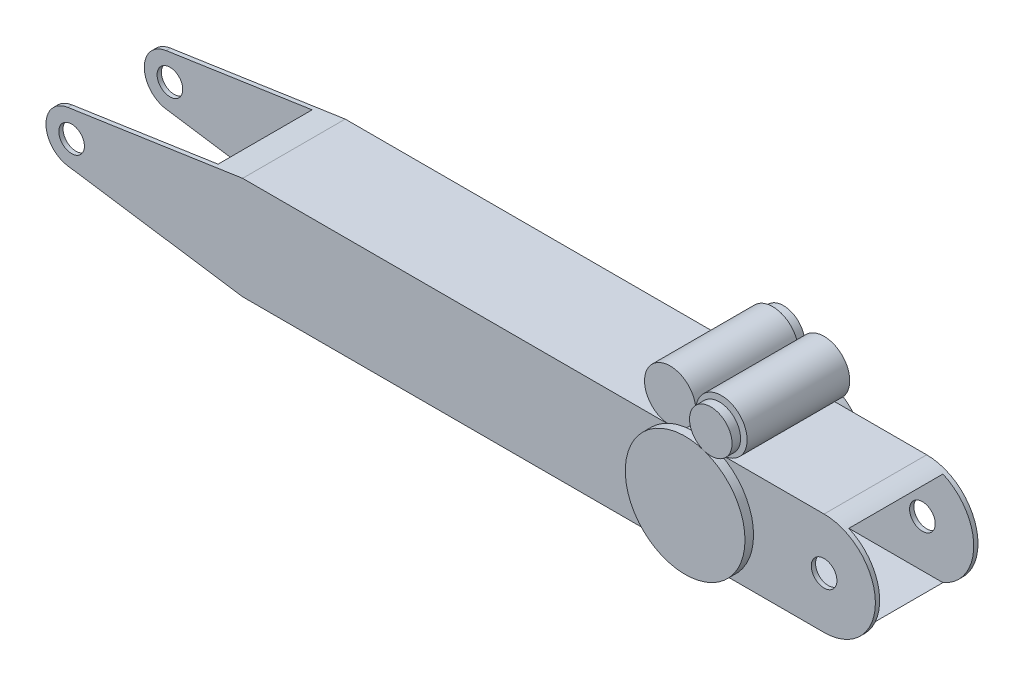
SolidWorks part; units mm, degrees
ref_plane "Front Plane" through (0, 0, 0) normal (0, 0, 1) x (1, 0, 0)
ref_plane "Top Plane" through (0, 0, 0) normal (0, 1, 0) x (1, 0, 0)
ref_plane "Right Plane" through (0, 0, 0) normal (1, 0, 0) x (0, 0, -1)
sketch "Sketch1" plane through (0, 0, 0) normal (0, 0, 1) x (1, 0, 0)
  line L0 (-282.1956, 18.8438) -> (-152.4, 38.1)
  line L1 (-152.4, -38.1) -> (279.4, -38.1)
  line L2 (-279.4, -38.1) -> (-279.4, 38.1) construction
  line L3 (-152.4, 38.1) -> (279.4, 38.1)
  line L4 (279.4, -38.1) -> (279.4, 38.1) construction
  line L5 (-279.4, -38.1) -> (279.4, 38.1) construction
  line L6 (-279.4, 38.1) -> (279.4, -38.1) construction
  line L7 (-282.1956, -18.8438) -> (-152.4, -38.1)
  line L8 (-279.4, 38.1) -> (-152.4, 38.1) construction
  line L9 (-279.4, -38.1) -> (-152.4, -38.1) construction
  circle A0 centre (279.4, 0) radius 9.525
  circle A1 centre (-279.4, 0) radius 9.525
  arc A2 (279.4, -38.1) -> (279.4, 38.1) centre (279.4, 0) ccw
  arc A3 (-282.1956, 18.8438) -> (-282.1956, -18.8438) centre (-279.4, 0) ccw
  arc A4 (-279.4, -19.05) -> (-279.4, 19.05) centre (-279.4, 0) ccw construction
  arc A5 (269.1988, 36.7089) -> (269.1988, -36.7089) centre (279.4, 0) ccw construction
  arc A6 (-279.4, 19.05) -> (-282.1956, 18.8438) centre (-279.4, 0) ccw construction
  arc A7 (-282.1956, -18.8438) -> (-279.4, -19.05) centre (-279.4, 0) ccw construction
  arc A8 (279.4, 38.1) -> (269.1988, 36.7089) centre (279.4, 0) ccw construction
  arc A9 (269.1988, -36.7089) -> (279.4, -38.1) centre (279.4, 0) ccw construction
  point P0 (0, 0)
  dimension "D3" = 19.05
  dimension "D4" = 38.1
  dimension "D1" = 558.8
  dimension "D2" = 76.2
  dimension "D5" = 127
extrude "Boss-Extrude1" add sketch "Sketch1" along normal mid plane 76.2
sketch "Sketch2" plane through (0, 0, 0) normal (1, 0, 0) x (0, 0, -1)
  line L8 (34.925, -34.925) -> (34.925, 34.925)
  line L9 (34.925, 34.925) -> (-34.925, 34.925)
  line L10 (-34.925, 34.925) -> (-34.925, -34.925)
  line L11 (-34.925, -34.925) -> (34.925, -34.925)
  line L12 (34.925, -34.925) -> (34.925, 34.925)
  line L13 (34.925, 34.925) -> (-34.925, 34.925)
  line L14 (-34.925, 34.925) -> (-34.925, -34.925)
  line L15 (-34.925, -34.925) -> (34.925, -34.925)
  dimension "D1" = 3.175
extrude "Cut-Extrude1" cut sketch "Sketch2" against normal through all both and the other way through all
sketch "Sketch3" plane through (0, 0, 38.1) normal (0, 0, 1) x (1, 0, 0)
  line L0 (279.4, 38.1) -> (-152.4, 38.1) construction
  circle A0 centre (165.1, 57.15) radius 19.05
  circle A1 centre (203.2, 57.15) radius 19.05
  circle A2 centre (279.4, 0) radius 9.525 construction
  circle M3 centre (279.4, 0) radius 9.525
  dimension "D1" = 38.1
  dimension "D2" = 76.2
extrude "Boss-Extrude2" add sketch "Sketch3" against normal up to surface (76.2 mm away) separate body contours A0 | A1 M3 up to face at (-48.0909, 0, -38.1)
sketch "Sketch4" plane through (0, 0, 38.1) normal (0, 0, 1) x (1, 0, 0)
  line L0 (184.15, -942.85) -> (184.15, 49057.15) construction
  circle A0 centre (184.15, 0) radius 44.45
  circle A3 centre (203.2, 57.15) radius 15.7914
  circle A4 centre (203.2, 57.15) radius 19.05
  circle A5 centre (203.2, 57.15) radius 19.05 construction
  line M4 (279.4, 38.1) -> (-152.4, 38.1)
  line M8 (-152.4, -38.1) -> (279.4, -38.1)
  dimension "D2" = 88.9
  dimension "D1" = 0
extrude "Boss-Extrude3" add sketch "Sketch4" along normal blind 6.35 from offset 1.5875 separate body contours A0 M4 M8 | A3 | A0 M4 | A0 M8
mirror "Mirror1" about plane through (0, 0, 0) normal (0, 0, 1) of bodies 106
sketch "Sketch5" plane through (0, 0, -38.1) normal (0, 0, -1) x (-1, 0, 0)
  circle A0 centre (-165.1, 57.15) radius 15.7914
  circle A1 centre (-165.1, 57.15) radius 19.05
  circle A2 centre (-165.1, 57.15) radius 19.05 construction
  circle A3 centre (-184.15, 0) radius 44.45 construction
  dimension "D1" = 0
extrude "Boss-Extrude4" add sketch "Sketch5" along normal up to surface (6.35 mm away) from surface at 1.5875 separate body up to face at (228.6, 0, -46.0375) starting at face at (228.6, 0, -39.6875)
